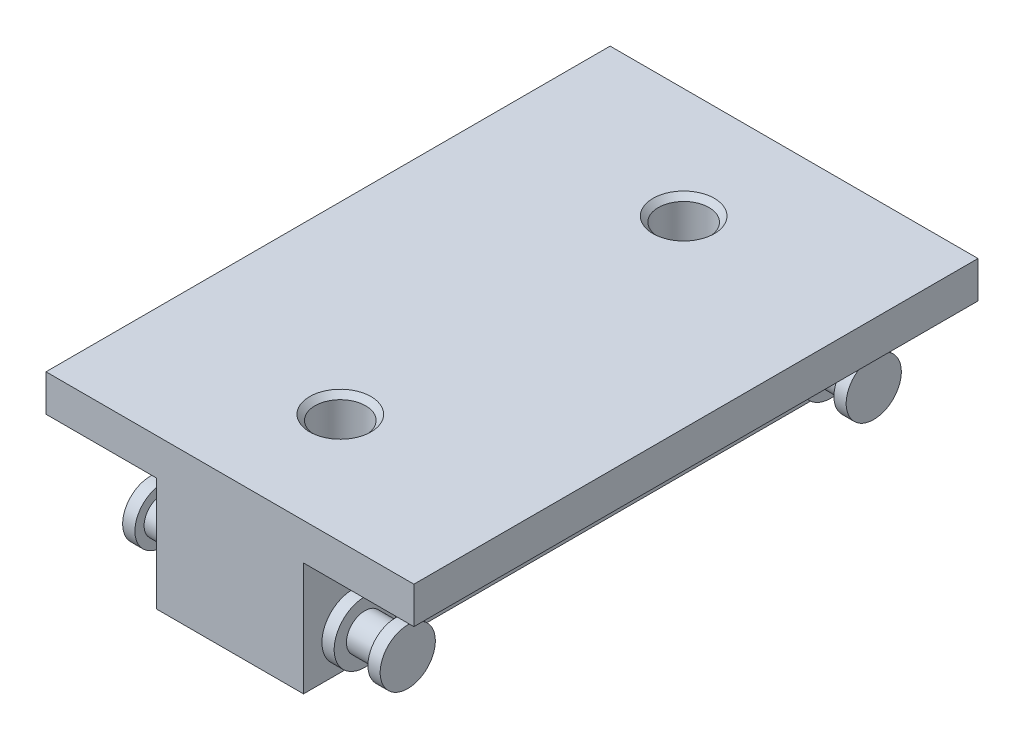
SolidWorks part; units mm, degrees
ref_plane "前视基准面" through (0, 0, 0) normal (0, 0, 1) x (1, 0, 0)
ref_plane "上视基准面" through (0, 0, 0) normal (0, 1, 0) x (1, 0, 0)
ref_plane "右视基准面" through (0, 0, 0) normal (1, 0, 0) x (0, 0, -1)
other "Configuration Table"
ref_plane "基准面1" through (0, -6, 0) normal (0, -1, 0) x (1, 0, 0)
sketch "草图1" plane through (0, -6, 0) normal (0, -1, 0) x (1, 0, 0)
  line L0 (-15, -23) -> (15, -23)
  line L1 (15, -23) -> (15, 23)
  line L2 (15, 23) -> (-15, 23)
  line L3 (-15, 23) -> (-15, -23)
extrude "凸台-拉伸1" add sketch "草图1" against normal blind 12.25
sketch "草图2" plane through (0, 0, -23) normal (0, 0, -1) x (-1, 0, 0)
  line L0 (6, 3.25) -> (6, -6)
  line L1 (6, -6) -> (15, -6)
  line L2 (15, -6) -> (15, 3.25)
  line L3 (15, 3.25) -> (6, 3.25)
extrude "切除-拉伸1" cut sketch "草图2" against normal through all
sketch "草图3" plane through (0, 0, -23) normal (0, 0, -1) x (-1, 0, 0)
  line L0 (-6, 3.25) -> (-15, 3.25)
  line L1 (-15, 3.25) -> (-15, -6)
  line L2 (-15, -6) -> (-6, -6)
  line L3 (-6, -6) -> (-6, 3.25)
extrude "切除-拉伸2" cut sketch "草图3" against normal through all
ref_plane "基准面2" through (0, 0, 19) normal (0, 0, 1) x (1, 0, 0)
sketch "草图4" plane through (0, 0, 19) normal (0, 0, 1) x (1, 0, 0)
  line L0 (6, -0.625) -> (6, -3.125)
  line L1 (6, -3.125) -> (10.5, -3.125)
  line L2 (10.5, -3.125) -> (10.5, -0.875)
  line L3 (10.5, -0.875) -> (9.5, -0.875)
  line L4 (9.5, -0.875) -> (9.5, -1.625)
  line L5 (9.5, -1.625) -> (7, -1.625)
  line L6 (7, -1.625) -> (7, -0.625)
  line L7 (7, -0.625) -> (6, -0.625)
  line L8 (6, -3.125) -> (10.5, -3.125) construction
revolve "旋转1" add sketch "草图4" angle 360 about L8
sketch "草图5" plane through (0, 0, 19) normal (0, 0, 1) x (1, 0, 0)
  line L0 (-10.5, -0.875) -> (-10.5, -3.125)
  line L1 (-10.5, -3.125) -> (-6, -3.125)
  line L2 (-6, -3.125) -> (-6, -0.625)
  line L3 (-6, -0.625) -> (-7, -0.625)
  line L4 (-7, -0.625) -> (-7, -1.625)
  line L5 (-7, -1.625) -> (-9.5, -1.625)
  line L6 (-9.5, -1.625) -> (-9.5, -0.875)
  line L7 (-9.5, -0.875) -> (-10.5, -0.875)
  line L8 (-10.5, -3.125) -> (-6, -3.125) construction
revolve "旋转2" add sketch "草图5" angle 360 about L8
ref_plane "基准面3" through (0, 0, -19) normal (0, 0, 1) x (1, 0, 0)
sketch "草图6" plane through (0, 0, -19) normal (0, 0, 1) x (1, 0, 0)
  line L0 (6, -0.625) -> (6, -3.125)
  line L1 (6, -3.125) -> (10.5, -3.125)
  line L2 (10.5, -3.125) -> (10.5, -0.875)
  line L3 (10.5, -0.875) -> (9.5, -0.875)
  line L4 (9.5, -0.875) -> (9.5, -1.625)
  line L5 (9.5, -1.625) -> (7, -1.625)
  line L6 (7, -1.625) -> (7, -0.625)
  line L7 (7, -0.625) -> (6, -0.625)
  line L8 (6, -3.125) -> (10.5, -3.125) construction
revolve "旋转3" add sketch "草图6" angle 360 about L8
sketch "草图7" plane through (0, 0, -19) normal (0, 0, 1) x (1, 0, 0)
  line L0 (-10.5, -0.875) -> (-10.5, -3.125)
  line L1 (-10.5, -3.125) -> (-6, -3.125)
  line L2 (-6, -3.125) -> (-6, -0.625)
  line L3 (-6, -0.625) -> (-7, -0.625)
  line L4 (-7, -0.625) -> (-7, -1.625)
  line L5 (-7, -1.625) -> (-9.5, -1.625)
  line L6 (-9.5, -1.625) -> (-9.5, -0.875)
  line L7 (-9.5, -0.875) -> (-10.5, -0.875)
  line L8 (-10.5, -3.125) -> (-6, -3.125) construction
revolve "旋转4" add sketch "草图7" angle 360 about L8
hole_wizard "M3.5 平头机械螺钉的锥形沉头孔1" positions "草图9" profile "草图8" countersink size "M3.5" standard "ANSI Metric"
sketch "草图9" plane through (0, -6, 0) normal (0, -1, 0) x (-1, 0, 0)
  point P0 (0, 14)
  point P1 (0, -14)
sketch "草图8" plane through (0, -6, -14) normal (1, 0, 0) x (0, 0, -1)
  line L0 (0, 0) -> (0, 12.25)
  line L1 (0, 12.25) -> (2.5, 12.25)
  line L2 (2.067, 11.817) -> (2.067, 0.433)
  line L3 (2.067, 0.433) -> (2.5, 0)
  line L5 (2.5, 0) -> (0, 0)
  line L6 (-2.067, 0.433) -> (-2.5, 0) construction
  line L7 (2.5, 12.25) -> (2.067, 11.817)
  line L8 (-2.5, 12.25) -> (-2.067, 11.817) construction
  line L11 (0, -6.35) -> (0, 107.95) construction
  dimension "通孔孔直径" = 4.134
  dimension "通孔孔深度" = 12.25
  dimension "近端锥形沉头孔直径" = 5
  dimension "近端锥形沉头孔角度" = 90
  dimension "远端锥形沉头孔直径" = 5
  dimension "远端锥形沉头孔角度" = 90
